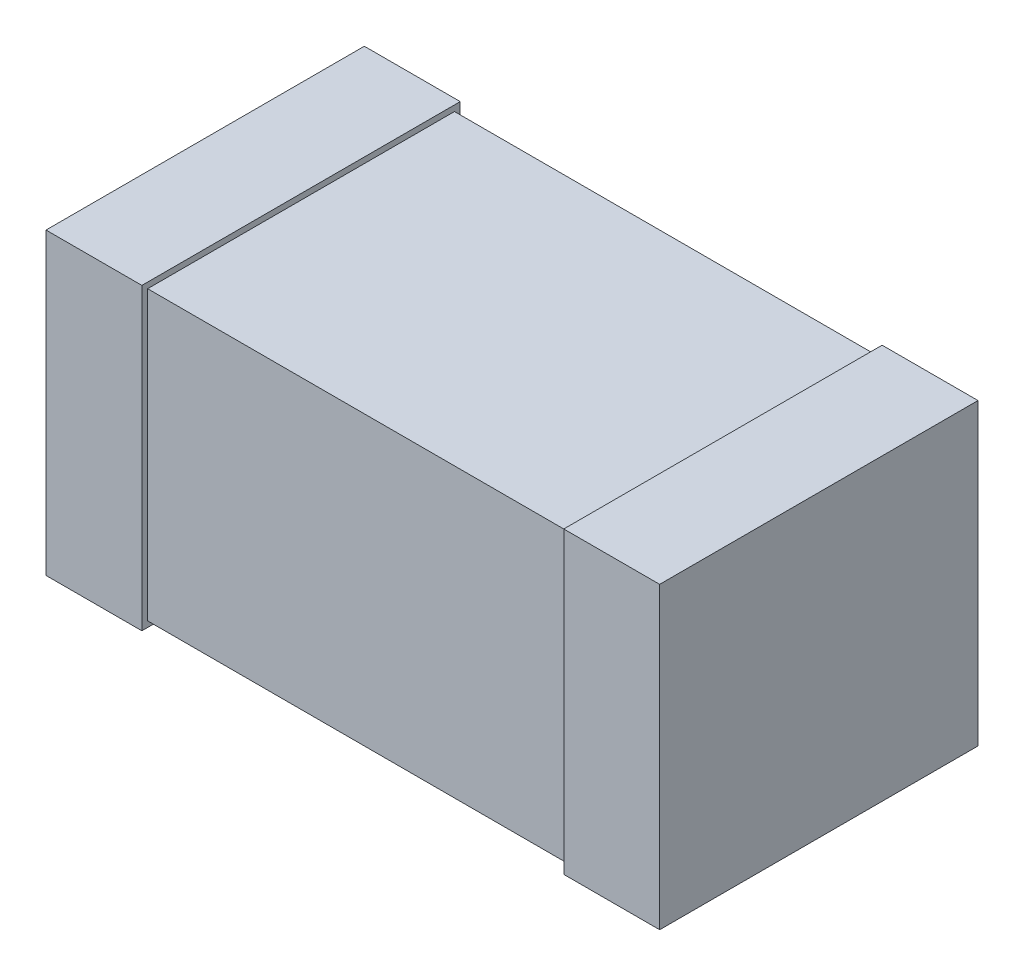
SolidWorks part; units mm, degrees
ref_plane "Front Plane" through (0, 0, 0) normal (0, 0, 1) x (1, 0, 0)
ref_plane "Top Plane" through (0, 0, 0) normal (0, 1, 0) x (1, 0, 0)
ref_plane "Right Plane" through (0, 0, 0) normal (1, 0, 0) x (0, 0, -1)
sketch "Sketch1" plane through (0, 0, 0) normal (0, 1, 0) x (1, 0, 0)
  line L1 (-1.6, 0.8) -> (1.6, 0.8)
  line L2 (-1.6, 0.8) -> (-1.6, -0.8)
  line L3 (-1.6, -0.8) -> (1.6, -0.8)
  line L4 (1.6, 0.8) -> (1.6, -0.8)
  point P4 (0, 0.8)
  point P6 (1.6, 0)
  dimension "D1" = 1.6
  dimension "D2" = 3.2
extrude "Extrude1" add sketch "Sketch1" along normal blind 1.5
sketch "Sketch2" plane through (0, 0, 0) normal (0, 0, 1) x (1, 0, 0)
  line L0 (-1.6, 1.5) -> (-1.6, 0) construction
  line L1 (-1.1, 1.53) -> (-1.6, 1.53)
  line L2 (-1.1, 1.53) -> (-1.1, -0.03)
  line L3 (-1.1, -0.03) -> (-1.6, -0.03)
  line L4 (-1.6, 1.53) -> (-1.6, -0.03)
  line L5 (-1.6, 1.5) -> (1.6, 1.5) construction
  line L6 (-1.6, 0) -> (1.6, 0) construction
  line L7 (0, 0) -> (0, -0.3575) construction
  line L8 (1.6, 1.53) -> (1.6, -0.03)
  line L9 (1.1, -0.03) -> (1.6, -0.03)
  line L10 (1.1, 1.53) -> (1.1, -0.03)
  line L11 (1.1, 1.53) -> (1.6, 1.53)
  dimension "D1" = 0.5
  dimension "D2" = 0.03
  dimension "D3" = 0.03
extrude "Extrude2" add sketch "Sketch2" along normal offset from surface 0.03 and the other way offset from surface (0.83 mm away) 0.03 up to face at (0, 0.75, 0.8) offset beyond the face yes other way up to face at (0, 0.75, -0.8)
ref_plane "Board Plane" through (0, -0.03, 0) normal (0, 1, 0) x (-1, 0, 0)
sketch "Component_Outline" plane through (0, -0.03, 0) normal (0, 1, 0) x (-1, 0, 0)
  line L1 (1.6, 0.83) -> (-1.6, 0.83)
  line L2 (1.6, 0.83) -> (1.6, -0.83)
  line L3 (1.6, -0.83) -> (-1.6, -0.83)
  line L4 (-1.6, 0.83) -> (-1.6, -0.83)
